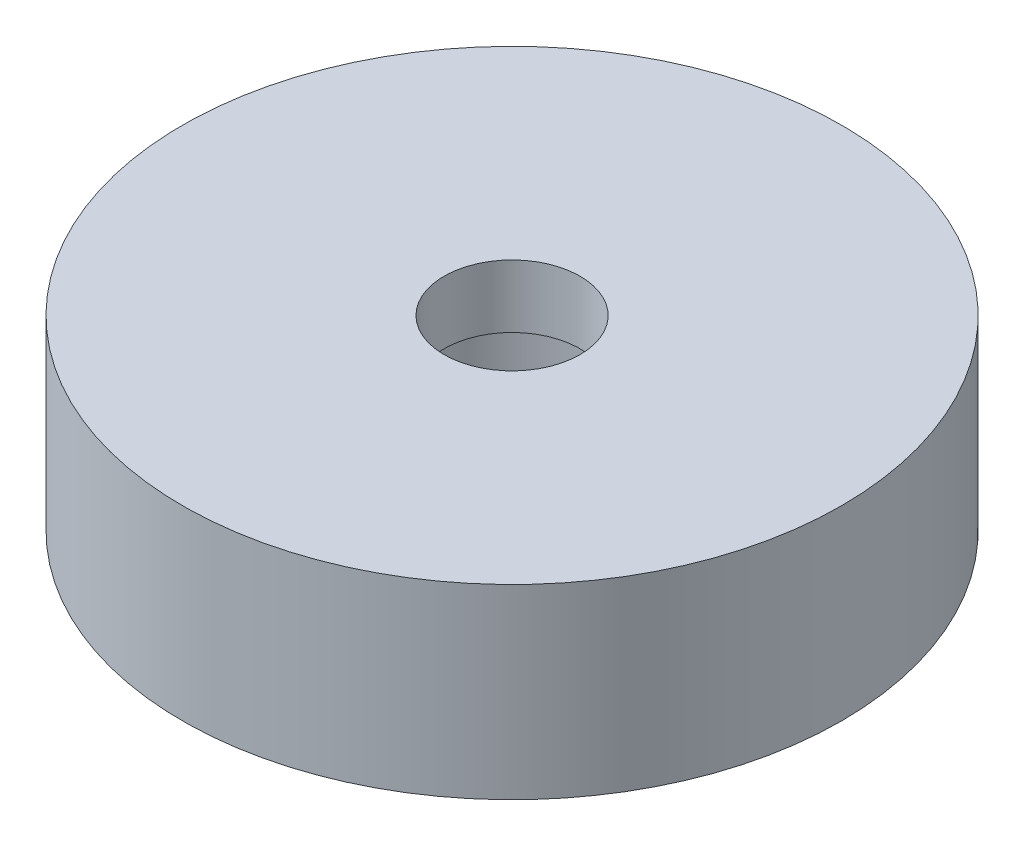
SolidWorks part; units mm, degrees
ref_plane "Front Plane" through (0, 0, 0) normal (0, 0, 1) x (1, 0, 0)
ref_plane "Top Plane" through (0, 0, 0) normal (0, 1, 0) x (1, 0, 0)
ref_plane "Right Plane" through (0, 0, 0) normal (1, 0, 0) x (0, 0, -1)
sketch "Sketch1" plane through (0, 0, 0) normal (0, 0, 1) x (1, 0, 0)
  line L0 (2.8, 0) -> (2.8, 3)
  line L1 (2.8, 3) -> (1.65, 3)
  line L2 (1.65, 3) -> (1.65, 4.525)
  line L3 (1.65, 4.525) -> (8, 4.525)
  line L4 (8, 4.525) -> (8, 0)
  line L5 (8, 0) -> (2.8, 0)
  line L6 (0, -251.4584) -> (0, 12321.463) construction
  point P3 (0, 0)
  dimension "D1" = 5.6
  dimension "D2" = 3.3
  dimension "D3" = 3
  dimension "D4" = 1.525
  dimension "D5" = 16
revolve "Revolve1" add sketch "Sketch1" angle 360 about L6
